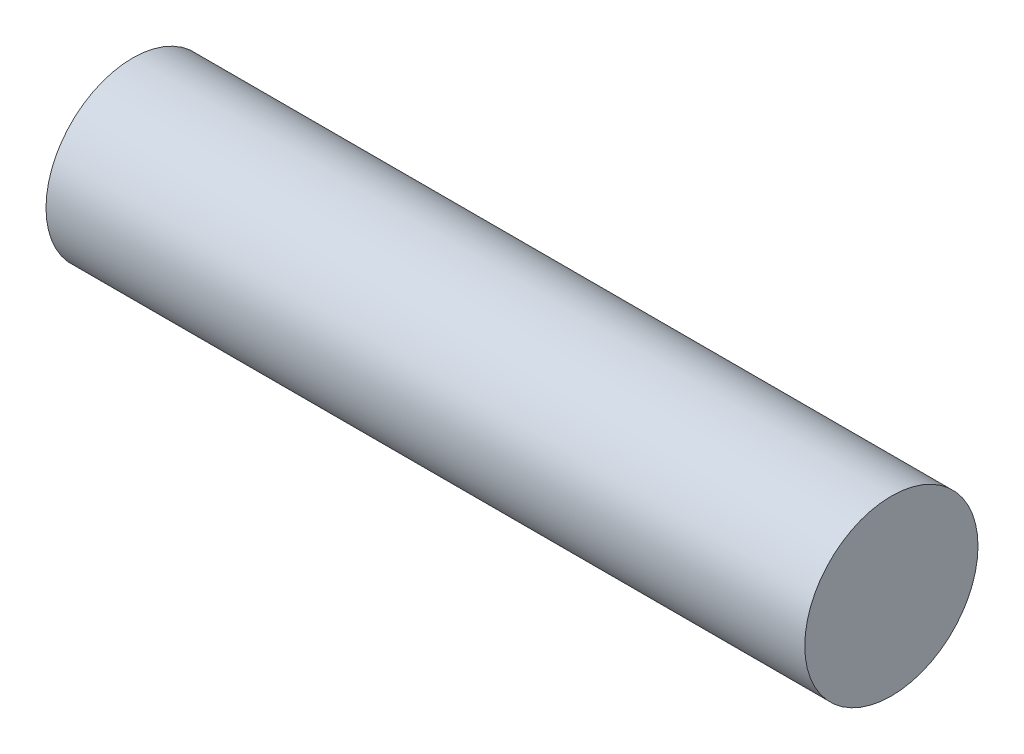
SolidWorks part; units mm, degrees
ref_plane "Front Plane" through (0, 0, 0) normal (0, 0, 1) x (1, 0, 0)
ref_plane "Top Plane" through (0, 0, 0) normal (0, 1, 0) x (1, 0, 0)
ref_plane "Right Plane" through (0, 0, 0) normal (1, 0, 0) x (0, 0, -1)
sketch "Sketch1" plane through (0, 0, 0) normal (1, 0, 0) x (0, 0, -1)
  circle A0 centre (0, 0) radius 6.35
  dimension "D1" = 12.7
extrude "Boss-Extrude1" add sketch "Sketch1" along normal blind 55.626
sketch "Sketch2" plane through (0, 0, 0) normal (-1, 0, 0) x (0, 0, 1)
  circle A0 centre (0, 0) radius 3.1788
  dimension "D1" = 6.3576
extrude "Cut-Extrude1" cut sketch "Sketch2" against normal blind 12.7
